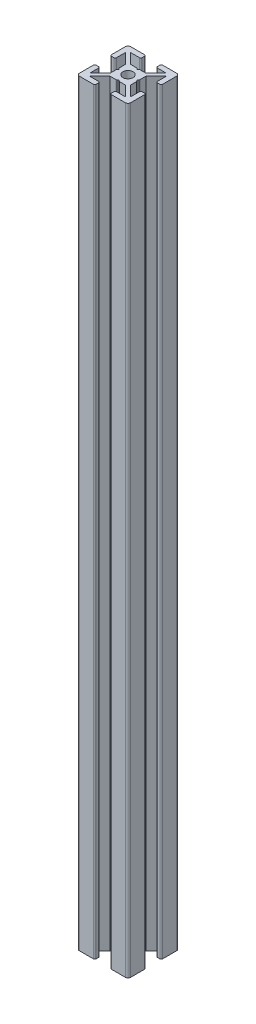
SolidWorks part; units mm, degrees
ref_plane "Front Plane" through (0, 0, 0) normal (0, 0, 1) x (1, 0, 0)
ref_plane "Top Plane" through (0, 0, 0) normal (0, 1, 0) x (1, 0, 0)
ref_plane "Right Plane" through (0, 0, 0) normal (1, 0, 0) x (0, 0, -1)
sketch "Sketch1" plane through (0, 0, 0) normal (0, 1, 0) x (1, 0, 0)
  line L0 (7, 20) -> (7, 18)
  line L1 (0, 0) -> (20, 0)
  line L2 (0, 0) -> (0, 20)
  line L3 (0, 20) -> (20, 20)
  line L4 (20, 0) -> (20, 20)
  line L5 (7, 18) -> (3, 18)
  line L6 (3, 18) -> (7, 14)
  line L7 (7, 14) -> (13, 14)
  line L8 (13, 14) -> (17, 18)
  line L9 (17, 18) -> (13, 18)
  line L10 (13, 18) -> (13, 20)
  line L11 (13, 20) -> (7, 20)
  line L12 (20, 7) -> (20, 13)
  line L13 (20, 13) -> (18, 13)
  line L14 (18, 13) -> (18, 17)
  line L15 (18, 17) -> (14, 13)
  line L16 (14, 13) -> (14, 7)
  line L17 (14, 7) -> (18, 3)
  line L18 (18, 3) -> (18, 7)
  line L19 (18, 7) -> (20, 7)
  line L20 (7, 0) -> (13, 0)
  line L21 (13, 0) -> (13, 2)
  line L22 (13, 2) -> (17, 2)
  line L23 (17, 2) -> (13, 6)
  line L24 (13, 6) -> (7, 6)
  line L25 (7, 6) -> (3, 2)
  line L26 (3, 2) -> (7, 2)
  line L27 (7, 2) -> (7, 0)
  line L28 (0, 13) -> (0, 7)
  line L29 (0, 7) -> (2, 7)
  line L30 (2, 7) -> (2, 3)
  line L31 (2, 3) -> (6, 7)
  line L32 (6, 7) -> (6, 13)
  line L33 (6, 13) -> (2, 17)
  line L34 (2, 17) -> (2, 13)
  line L35 (2, 13) -> (0, 13)
  line L36 (9.5, 14) -> (10.5, 14)
  line L37 (10.5, 14) -> (10, 13.5)
  line L38 (10, 13.5) -> (9.5, 14)
  line L39 (13.5, 10) -> (14, 10.5)
  line L40 (14, 10.5) -> (14, 9.5)
  line L41 (14, 9.5) -> (13.5, 10)
  line L42 (10, 6.5) -> (10.5, 6)
  line L43 (10.5, 6) -> (9.5, 6)
  line L44 (9.5, 6) -> (10, 6.5)
  line L45 (6.5, 10) -> (6, 9.5)
  line L46 (6, 9.5) -> (6, 10.5)
  line L47 (6, 10.5) -> (6.5, 10)
  circle A0 centre (10, 10) radius 2
  point P10 (10, 10)
  point P41 (10, 10)
  point P43 (10, 14)
  point P57 (10, 10)
  dimension "D8" = 4
  dimension "D1" = 20
  dimension "D2" = 20
  dimension "D3" = 7
  dimension "D4" = 7
  dimension "D5" = 6
  dimension "D6" = 4
  dimension "D7" = 4
  dimension "D9" = 0.5
  dimension "D11" = 0.5
  dimension "D12" = 0.5
  dimension "D13" = 4
  dimension "D10" = 4
extrude "Boss-Extrude1" add sketch "Sketch1" along normal blind 296 contours L35 L34 L33 L32 L31 L30 L29 L2 L1 L27 L26 L25 L24 L23 L22 L21 L4 L19 L18 L17 L16 L15 L14 L13 L3 L10 L9 L8 L7 L6 L5 L0 A0
fillet "Fillet1" radius 1 4 edges at (0, 148, -20) (0, 148, 0) (20, 148, 0) (20, 148, -20)
fillet "Fillet2" radius 0.5 16 edges at (20, 148, -13) (18, 148, -13) (20, 148, -7) (18, 148, -7) (13, 148, -2) (13, 148, 0) (7, 148, 0) (7, 148, -2) (0, 148, -7) (2, 148, -7) (13, 148, -20) (13, 148, -18) (7, 148, -20) (7, 148, -18) (0, 148, -13) (2, 148, -13)
fillet "Fillet4" radius 0.5 8 edges at (10.5, 148, -6) (9.5, 148, -6) (6, 148, -9.5) (6, 148, -10.5) (10.5, 148, -14) (9.5, 148, -14) (14, 148, -9.5) (14, 148, -10.5)
